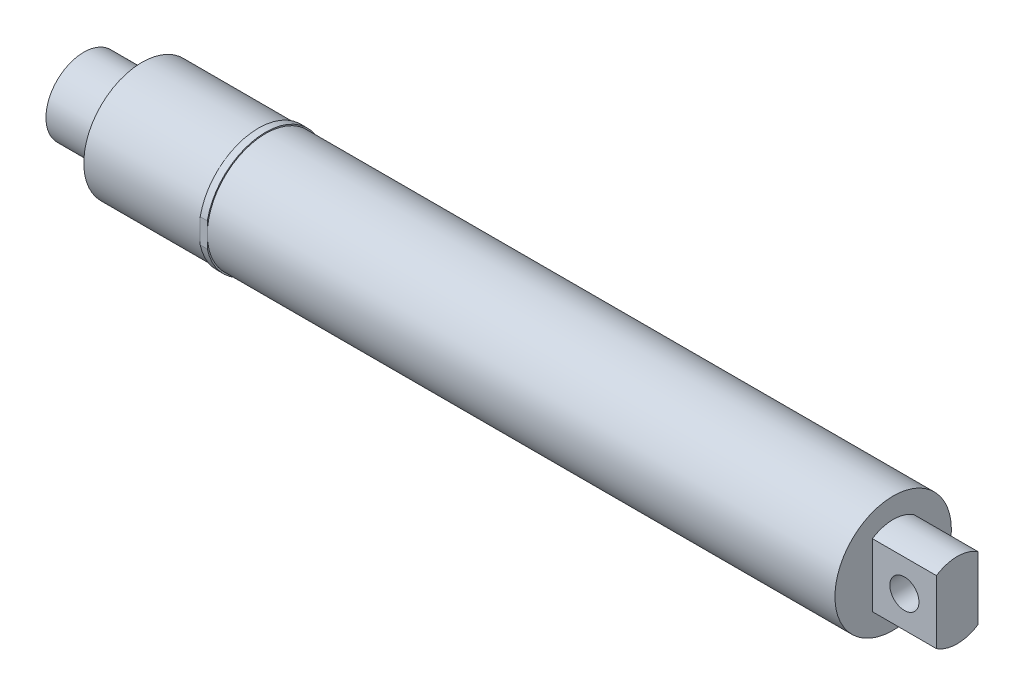
SolidWorks part; units mm, degrees
ref_plane "Alzado" through (0, 0, 0) normal (0, 0, 1) x (1, 0, 0)
ref_plane "Planta" through (0, 0, 0) normal (0, 1, 0) x (1, 0, 0)
ref_plane "Vista lateral" through (0, 0, 0) normal (1, 0, 0) x (0, 0, -1)
sketch "Croquis2" plane through (0, 0, 0) normal (1, 0, 0) x (0, 0, -1)
  circle A0 centre (0, 0) radius 12.7
  dimension "D1" = 25.4
extrude "Saliente-Extruir1" add sketch "Croquis2" along normal blind 190.5
sketch "Croquis3" plane through (0, 0, 0) normal (1, 0, 0) x (0, 0, -1)
  circle A0 centre (0, 0) radius 8.255
  circle A1 centre (0, 0) radius 12.7
  dimension "D1" = 16.51
  dimension "D2" = 25.4
extrude "Cortar-Extruir1" cut sketch "Croquis3" along normal blind 12.7
sketch "Croquis4" plane through (0, 0, 0) normal (-1, 0, 0) x (0, 0, 1)
  circle A0 centre (0, 0) radius 2.54
  dimension "D1" = 5.08
extrude "Cortar-Extruir2" cut sketch "Croquis4" against normal blind 170.18
ref_plane "Plano1" through (193.04, 0, 0) normal (1, 0, 0) x (0, 0, -1)
sketch "Croquis6" plane through (193.04, 0, 0) normal (1, 0, 0) x (0, 0, -1)
  circle A0 centre (0, 0) radius 12.7
  circle A1 centre (0, 0) radius 8.255
  dimension "D1" = 25.4
  dimension "D2" = 16.51
extrude "Cortar-Extruir6" cut sketch "Croquis6" against normal blind 16.51
ref_plane "Plano2" through (193.04, 0, 0) normal (1, 0, 0) x (0, 0, -1)
sketch "Croquis8" plane through (193.04, 0, 0) normal (1, 0, 0) x (0, 0, -1)
  line L0 (-4.533, 6.899) -> (-4.533, -6.899)
  line L1 (0, 4.1045) -> (0, -4.3693) construction
  line L2 (4.533, 6.899) -> (4.533, -6.899)
  arc A0 (-4.533, 6.899) -> (-4.533, -6.899) centre (0, 0) ccw
  arc A1 (-4.533, 6.899) -> (-4.533, -6.899) centre (0, 0) ccw construction
  arc A2 (4.533, 6.899) -> (4.533, -6.899) centre (0, 0) cw
extrude "Cortar-Extruir8" cut sketch "Croquis8" against normal blind 16.51
sketch "Croquis9" plane through (0, 0, -4.533) normal (0, 0, -1) x (-1, 0, 0)
  circle A0 centre (-183.515, 0) radius 3.175
  dimension "D1" = 6.35
extrude "Cortar-Extruir9" cut sketch "Croquis9" against normal blind 16.51
sketch "Croquis10" plane through (0, 0, 0) normal (0, 0, 1) x (1, 0, 0)
  line L0 (39.6461, -12.441) -> (39.6461, 12.959)
  line L2 (38.1, -12.441) -> (38.1, 12.959)
  line L3 (38.1, 12.959) -> (39.6461, 12.959)
  line L4 (38.1, -12.441) -> (39.6461, -12.441)
  dimension "D1" = 25.4
extrude "Saliente-Extruir2" add sketch "Croquis10" against normal blind 12.7 and the other way blind 12.7
sketch "Croquis12" plane through (0, 0, 0) normal (1, 0, 0) x (0, 0, -1)
  line L0 (0, 12.959) -> (-12.7, 12.959)
  line L1 (-12.7, 12.959) -> (12.7, 12.959) construction
  line L2 (-12.7, 12.959) -> (-12.7, 2.578)
  line L3 (-12.7, 12.959) -> (-12.7, 0) construction
  arc A0 (0, 12.959) -> (-12.7, 2.578) centre (0, 0) ccw
extrude "Cortar-Extruir10" cut sketch "Croquis12" along normal blind 64.262
sketch "Croquis13" plane through (38.1, 0, 0) normal (-1, 0, 0) x (0, 0, 1)
  line L0 (-12.7, 12.959) -> (-12.7, 0) construction
  line L1 (-12.7, 2.578) -> (-12.7, 12.959)
  line L2 (-12.7, 12.959) -> (0, 12.959)
  arc A0 (0, 12.959) -> (-12.7, 2.578) centre (0, 0) ccw
extrude "Cortar-Extruir11" cut sketch "Croquis13" against normal blind 64.262
sketch "Croquis14" plane through (38.1, 0, 0) normal (-1, 0, 0) x (0, 0, 1)
  line L0 (12.7, 0) -> (12.7, -12.441) construction
  line L1 (12.7, -2.7685) -> (12.7, -12.441)
  line L2 (12.7, -12.441) -> (3.7651, -12.441)
  line L3 (12.7, -12.441) -> (2.5519, -12.441) construction
  line L4 (-12.7695, -2.428) -> (-12.7, -12.441)
  line L5 (-12.7, -12.441) -> (-3.7651, -12.441)
  line L6 (-2.5519, -12.441) -> (-12.7, -12.441) construction
  arc A0 (12.7, -2.7685) -> (3.7651, -12.441) centre (0, 0) cw
  arc A1 (-3.7651, -12.441) -> (-12.7695, -2.428) centre (0, 0) cw
extrude "Cortar-Extruir12" cut sketch "Croquis14" against normal blind 64.262
